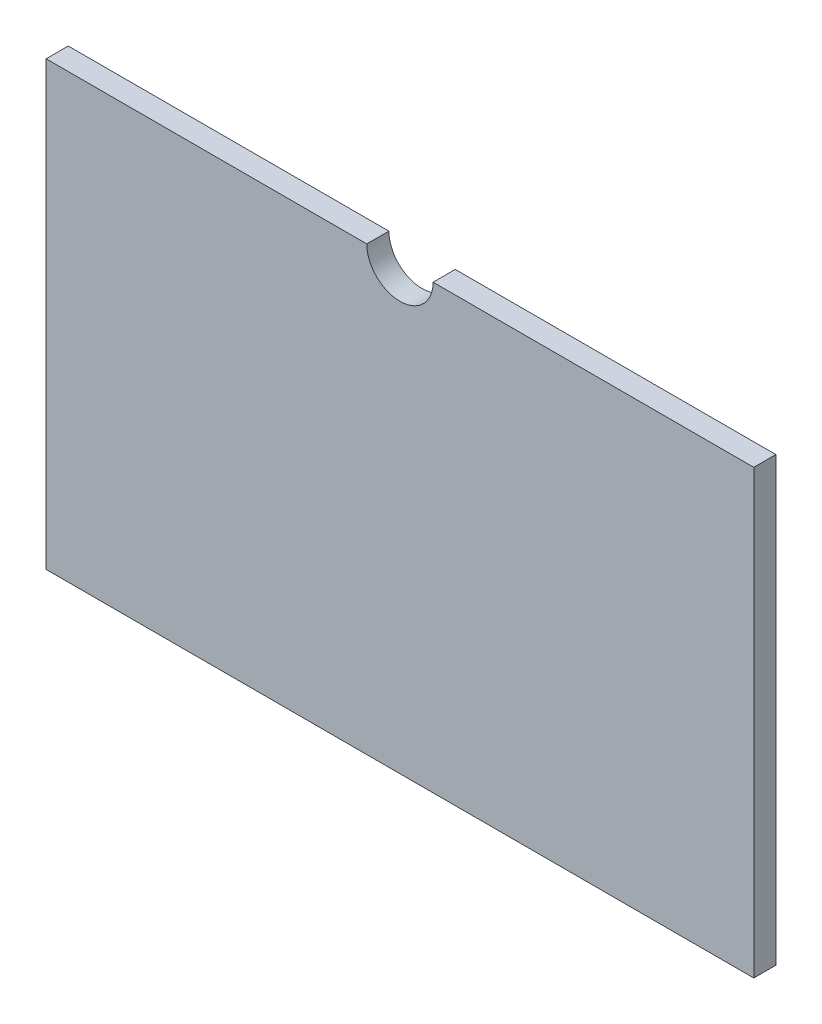
SolidWorks part; units mm, degrees
material "Plain Carbon Steel"
ref_plane "Front Plane" through (0, 0, 0) normal (0, 0, 1) x (1, 0, 0)
ref_plane "Top Plane" through (0, 0, 0) normal (0, 1, 0) x (1, 0, 0)
ref_plane "Right Plane" through (0, 0, 0) normal (1, 0, 0) x (0, 0, -1)
sketch "Sketch1" plane through (0, 0, 0) normal (0, 0, 1) x (1, 0, 0)
  line L0 (0, 0) -> (0, 100) construction
  line L1 (-160, 100) -> (-15, 100)
  line L2 (-160, 100) -> (-160, -100)
  line L3 (-160, -100) -> (160, -100)
  line L4 (160, 100) -> (160, -100)
  line L5 (-160, 0) -> (160, 0) construction
  line L6 (15, 100) -> (160, 100)
  line L7 (-15, 100) -> (15, 100) construction
  arc A0 (15, 100) -> (-15, 100) centre (0, 100) cw
  dimension "D3" = 15
  dimension "D1" = 320
  dimension "D2" = 200
  dimension "D4" = 160
extrude "Bottom Center Casing" add sketch "Sketch1" along normal blind 10
sketch "Sketch2" plane through (0, 0, 10) normal (0, 0, 1) x (1, 0, 0)
  line L0 (-15, 100) -> (-160, 100) construction
  line L1 (160, 100) -> (15, 100) construction
  line L2 (0, 100) -> (0, 66.7) construction
  line L3 (-87.5, 100) -> (87.5, 100) construction
  point P0 (-87.5, 100)
  point P3 (-87.5, 100)
  point P4 (87.5, 100)
  point P7 (87.5, 100)
  point P12 (0, 100)
  dimension "D1" = 33.3
